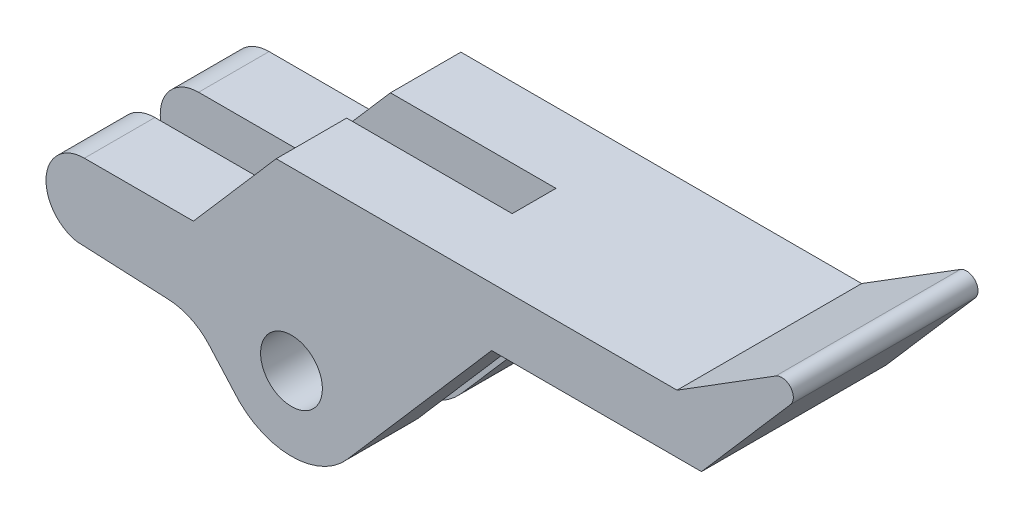
SolidWorks part; units mm, degrees
ref_plane "Front Plane" through (0, 0, 0) normal (0, 0, 1) x (1, 0, 0)
ref_plane "Top Plane" through (0, 0, 0) normal (0, 1, 0) x (1, 0, 0)
ref_plane "Right Plane" through (0, 0, 0) normal (1, 0, 0) x (0, 0, -1)
sketch "Sketch1" plane through (0, 0, 0) normal (0, 0, 1) x (1, 0, 0)
  line L0 (0, 0) -> (5.1406, 3.209)
  line L1 (5.9116, 2.3068) -> (1.2733, -3.04)
  line L2 (1.2733, -3.04) -> (-9.6567, -3.04)
  line L3 (-9.6567, -3.04) -> (-17.1685, -11.6994)
  line L8 (-30.8717, -4.9704) -> (-25.1917, -4.9704)
  line L9 (-25.1917, -4.9704) -> (-20.88, 0)
  line L10 (-20.88, 0) -> (0, 0)
  line L13 (-31.2857, -8.9271) -> (-26.4704, -9.1529)
  line L14 (-23.0815, -11.6023) -> (-24.3702, -10.1548)
  arc A0 (5.1406, 3.209) -> (5.9116, 2.3068) centre (5.4584, 2.7) cw
  arc A1 (-31.2857, -8.9271) -> (-30.8717, -4.9704) centre (-30.8717, -6.9704) cw
  circle A2 centre (-20.0843, -9.17) radius 1.61
  arc A3 (-23.0815, -11.6023) -> (-17.1685, -11.6994) centre (-20.0843, -9.17) ccw
  arc A4 (-26.4704, -9.1529) -> (-24.3702, -10.1548) centre (-26.6109, -12.1496) cw
  point P6 (0, 0)
  point P14 (8.529, 5.3241)
  point P18 (-26.615, -9.3648)
  point P22 (0, 0)
  point P23 (-24.7696, -10.1478)
  dimension "D7" = 0.6
  dimension "D5" = 6.06
  dimension "D9" = 2
  dimension "D11" = 3.22
  dimension "D12" = 3
  dimension "D14" = 3.86
  dimension "D1" = 3.04
  dimension "D2" = 10.47
  dimension "D3" = 20.88
  dimension "D4" = 10.93
  dimension "D6" = 6.58
  dimension "D8" = 2.7
  dimension "D10" = 5.68
  dimension "D13" = 9.17
extrude "Boss-Extrude1" add sketch "Sketch1" along normal blind 9.62
sketch "Sketch2" plane through (-4.0054, 3.4746, 0) normal (0.7554, -0.6553, 0) x (0, 0, -1)
  line L0 (-9.62, -8.6242) -> (0, -8.6242) construction
  line L1 (-3.67, -8.6242) -> (-5.95, -8.6242)
  line L2 (-3.67, -8.6242) -> (-3.67, -27.6318)
  line L3 (-3.67, -27.6318) -> (-5.95, -27.6318)
  line L4 (-5.95, -8.6242) -> (-5.95, -27.6318)
  line L5 (0, -20.0877) -> (0, -8.6242) construction
  line L6 (-9.62, -20.0877) -> (-9.62, -8.6242) construction
  dimension "D1" = 3.67
  dimension "D2" = 3.67
extrude "Cut-Extrude1" cut sketch "Sketch2" against normal up to surface up to face at (-4.1917, -3.04, 4.81)
sketch "Sketch3" plane through (0, -3.04, 0) normal (0, -1, 0) x (1, 0, 0)
  line L0 (-23.5171, 3.67) -> (-9.6567, 3.67) construction
  line L1 (-23.5171, 5.95) -> (-12.2567, 5.95)
  line L2 (-23.5171, 5.95) -> (-23.5171, 3.67)
  line L3 (-23.5171, 3.67) -> (-12.2567, 3.67)
  line L4 (-12.2567, 5.95) -> (-12.2567, 3.67)
  line L5 (-9.6567, 9.62) -> (-9.6567, 5.95) construction
  dimension "D1" = 2.6
extrude "Cut-Extrude2" cut sketch "Sketch3" against normal up to surface (3.04 mm away) up to face at (-10.44, 0, 4.81)
